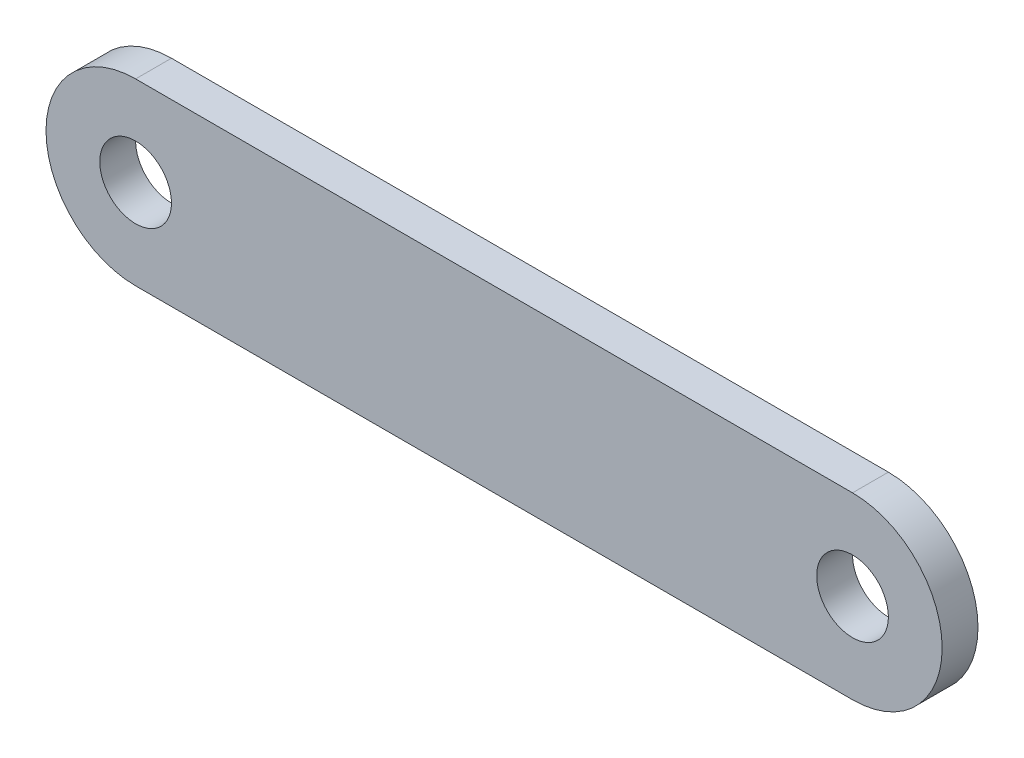
SolidWorks part; units mm, degrees
ref_plane "Спереди" through (0, 0, 0) normal (0, 0, 1) x (1, 0, 0)
ref_plane "Сверху" through (0, 0, 0) normal (0, 1, 0) x (1, 0, 0)
ref_plane "Справа" through (0, 0, 0) normal (1, 0, 0) x (0, 0, -1)
sketch "Эскиз1" plane through (0, 0, 0) normal (0, 0, 1) x (1, 0, 0)
  line L0 (0, 25) -> (200, 25)
  line L2 (0, -25) -> (200, -25)
  arc A4 (0, 25) -> (0, -25) centre (0, 0) ccw
  circle A5 centre (0, 0) radius 10
  circle A6 centre (200, 0) radius 10
  arc A7 (200, -25) -> (200, 25) centre (200, 0) ccw
  dimension "D1" = 50
  dimension "D2" = 20
  dimension "D3" = 200
extrude "Бобышка-Вытянуть2" add sketch "Эскиз1" along normal blind 10 contours A7 L0 A4 L2
sketch "Эскиз2" plane through (0, 0, 10) normal (0, 0, 1) x (1, 0, 0)
  circle A0 centre (0, 0) radius 10
  circle A1 centre (200, 0) radius 10
  dimension "D1" = 200
extrude "Вырез-Вытянуть2" cut sketch "Эскиз2" against normal blind 10
